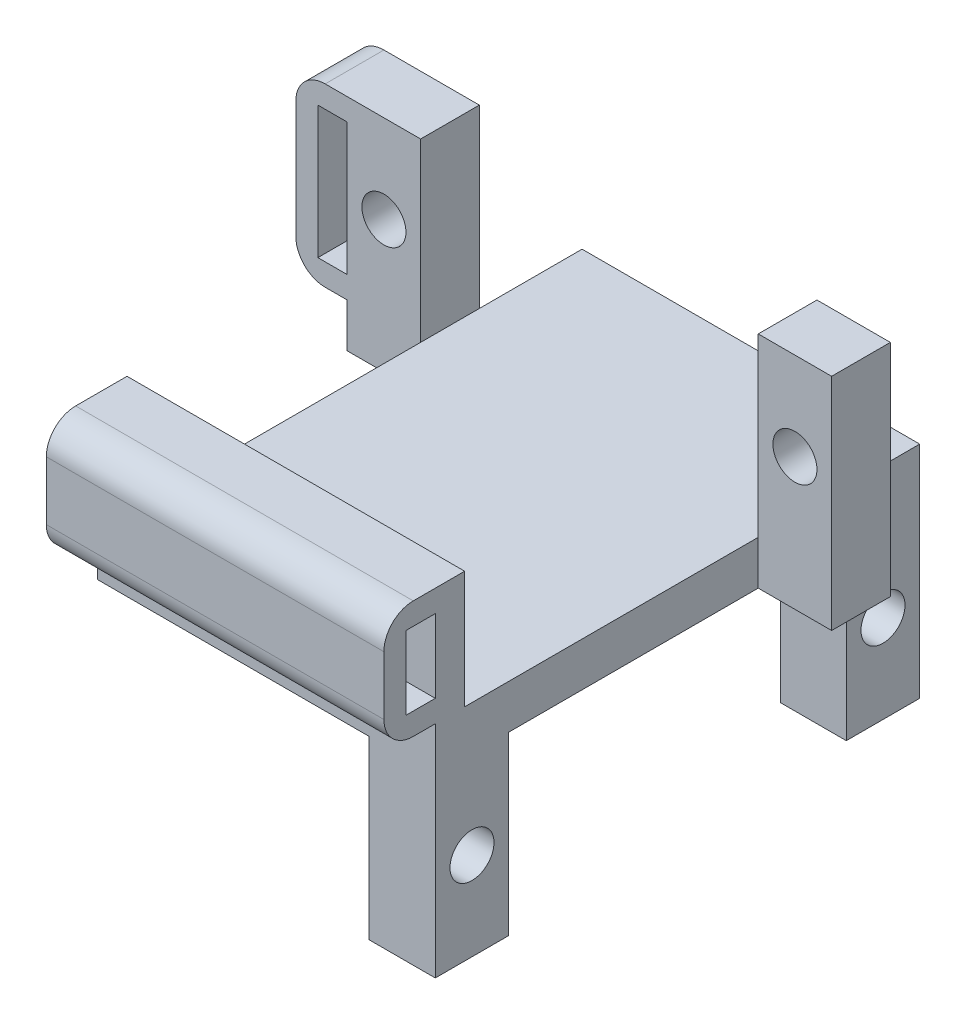
SolidWorks part; units mm, degrees
ref_plane "Front Plane" through (0, 0, 0) normal (0, 0, 1) x (1, 0, 0)
ref_plane "Top Plane" through (0, 0, 0) normal (0, 1, 0) x (1, 0, 0)
ref_plane "Right Plane" through (0, 0, 0) normal (1, 0, 0) x (0, 0, -1)
sketch "Sketch1" plane through (0, 0, 0) normal (0, 1, 0) x (1, 0, 0)
  line L2 (-14.8026, 11.5891) -> (-14.8026, -10.4109)
  line L3 (-14.8026, -10.4109) -> (8.1974, -10.4109)
  line L4 (8.1974, 11.5891) -> (8.1974, -10.4109)
  line L5 (8.1974, 15.5891) -> (13.1974, 15.5891)
  line L7 (8.1974, 11.5891) -> (13.1974, 11.5891)
  line L8 (13.1974, 15.5891) -> (13.1974, 11.5891)
  line L9 (-14.8026, 15.5891) -> (-19.8026, 15.5891)
  line L11 (-14.8026, 11.5891) -> (-19.8026, 11.5891)
  line L12 (-19.8026, 15.5891) -> (-19.8026, 11.5891)
  line L14 (-14.8026, 15.5891) -> (-14.8026, 22.5891)
  line L15 (-14.8026, 22.5891) -> (8.1974, 22.5891)
  line L16 (8.1974, 15.5891) -> (8.1974, 22.5891)
  dimension "D1" = 23
  dimension "D2" = 11
  dimension "D3" = 5
  dimension "D4" = 4
  dimension "D5" = 5
  dimension "D6" = 4
  dimension "D8" = 33
extrude "Boss-Extrude1" add sketch "Sketch1" along normal blind 3
sketch "Sketch4" plane through (0, 0, 0) normal (0, -1, 0) x (1, 0, 0)
  line L1 (8.1974, -22.5891) -> (3.6974, -22.5891)
  line L2 (8.1974, -22.5891) -> (8.1974, -17.5891)
  line L3 (8.1974, -17.5891) -> (3.6974, -17.5891)
  line L4 (3.6974, -22.5891) -> (3.6974, -17.5891)
  line L9 (8.1974, 10.4109) -> (3.6974, 10.4109)
  line L10 (8.1974, 10.4109) -> (8.1974, 5.4109)
  line L11 (8.1974, 5.4109) -> (3.6974, 5.4109)
  line L12 (3.6974, 10.4109) -> (3.6974, 5.4109)
  dimension "D1" = 5
  dimension "D2" = 4.5
  dimension "D3" = 5
  dimension "D4" = 4.5
extrude "Boss-Extrude3" add sketch "Sketch4" along normal blind 12
sketch "Sketch5" plane through (0, 3, 0) normal (0, 1, 0) x (1, 0, 0)
  line L1 (-19.8026, 15.5891) -> (-14.8026, 15.5891)
  line L2 (-19.8026, 15.5891) -> (-19.8026, 11.5891)
  line L3 (-19.8026, 11.5891) -> (-14.8026, 11.5891)
  line L4 (-14.8026, 15.5891) -> (-14.8026, 11.5891)
  line L5 (13.1974, 15.5891) -> (8.1974, 15.5891)
  line L6 (13.1974, 15.5891) -> (13.1974, 11.5891)
  line L7 (13.1974, 11.5891) -> (8.1974, 11.5891)
  line L8 (8.1974, 15.5891) -> (8.1974, 11.5891)
extrude "Boss-Extrude4" add sketch "Sketch5" along normal blind 12
sketch "Sketch6" plane through (0, 0, -11.5891) normal (0, 0, 1) x (1, 0, 0)
  line L0 (-19.8026, 15) -> (-14.8026, 3) construction
  line L1 (8.1974, 3) -> (13.1974, 15) construction
  circle A0 centre (-17.3026, 9) radius 1.5
  circle A1 centre (10.6974, 9) radius 1.5
  dimension "D1" = 3
  dimension "D2" = 3
extrude "Cut-Extrude1" cut sketch "Sketch6" against normal blind 10
sketch "Sketch7" plane through (8.1974, 0, 0) normal (1, 0, 0) x (0, 0, -1)
  line L0 (-5.4109, 0) -> (-10.4109, -12) construction
  line L1 (17.5891, 0) -> (22.5891, -12) construction
  circle A0 centre (-7.9109, -6) radius 1.5
  circle A1 centre (20.0891, -6) radius 1.5
  dimension "D1" = 3
  dimension "D2" = 3
extrude "Cut-Extrude2" cut sketch "Sketch7" against normal blind 10
sketch "Sketch8" plane through (0, 3, 0) normal (0, 1, 0) x (1, 0, 0)
  line L0 (8.1974, -10.4109) -> (8.1974, 11.5891) construction
  line L1 (-14.8026, -10.4109) -> (8.1974, -10.4109)
  line L2 (-14.8026, -10.4109) -> (-14.8026, -8.4109)
  line L3 (-14.8026, -8.4109) -> (8.1974, -8.4109)
  line L4 (8.1974, -10.4109) -> (8.1974, -8.4109)
  dimension "D1" = 2
extrude "Boss-Extrude5" add sketch "Sketch8" along normal blind 8
sketch "Sketch11" plane through (0, 0, 10.4109) normal (0, 0, 1) x (1, 0, 0)
  line L0 (-14.8026, 0) -> (-14.8026, 3) construction
  line L1 (8.1974, 11) -> (8.1974, -12) construction
  line L2 (-14.8026, 3) -> (8.1974, 3)
  line L3 (-14.8026, 3) -> (-14.8026, 11)
  line L4 (-14.8026, 11) -> (8.1974, 11)
  line L5 (8.1974, 3) -> (8.1974, 11)
  dimension "D1" = 3
  dimension "D2" = 8
extrude "Boss-Extrude7" add sketch "Sketch11" along normal blind 3.5
sketch "Sketch12" plane through (-14.8026, 0, 0) normal (-1, 0, 0) x (0, 0, 1)
  line L0 (8.4109, 11) -> (8.4109, 3) construction
  line L1 (10.4109, 9.5) -> (12.4109, 9.5)
  line L2 (10.4109, 9.5) -> (10.4109, 4.5)
  line L3 (10.4109, 4.5) -> (12.4109, 4.5)
  line L4 (12.4109, 9.5) -> (12.4109, 4.5)
  line L5 (13.9109, 3) -> (10.4109, 3) construction
  line L6 (8.4109, 11) -> (13.9109, 11) construction
  line L7 (13.9109, 11) -> (13.9109, 3) construction
  dimension "D1" = 2
  dimension "D2" = 1.5
  dimension "D3" = 1.5
  dimension "D4" = 1.5
extrude "Cut-Extrude3" cut sketch "Sketch12" against normal blind 27.5
fillet "Fillet1" radius 2 2 edges at (-3.3026, 3, 13.9109) (-3.3026, 11, 13.9109)
sketch "Sketch13" plane through (-19.8026, 0, 0) normal (-1, 0, 0) x (0, 0, 1)
  line L0 (-11.5891, 15) -> (-11.5891, 0) construction
  line L1 (-15.5891, 15) -> (-11.5891, 15)
  line L2 (-15.5891, 15) -> (-15.5891, 3)
  line L3 (-15.5891, 3) -> (-11.5891, 3)
  line L4 (-11.5891, 15) -> (-11.5891, 3)
  dimension "D1" = 12
extrude "Boss-Extrude8" add sketch "Sketch13" along normal blind 3.5
sketch "Sketch14" plane through (0, 0, -11.5891) normal (0, 0, 1) x (1, 0, 0)
  line L0 (-23.3026, 3) -> (-23.3026, 15) construction
  line L1 (-21.8026, 13.5) -> (-19.8026, 13.5)
  line L2 (-21.8026, 13.5) -> (-21.8026, 4.5)
  line L3 (-21.8026, 4.5) -> (-19.8026, 4.5)
  line L4 (-19.8026, 13.5) -> (-19.8026, 4.5)
  line L5 (-23.3026, 15) -> (-14.8026, 15) construction
  line L6 (-23.3026, 3) -> (-19.8026, 3) construction
  dimension "D1" = 1.5
  dimension "D2" = 1.5
  dimension "D3" = 1.5
  dimension "D4" = 2
extrude "Cut-Extrude4" cut sketch "Sketch14" against normal blind 10
fillet "Fillet2" radius 2 2 edges at (-23.3026, 3, -13.5891) (-23.3026, 15, -13.5891)
